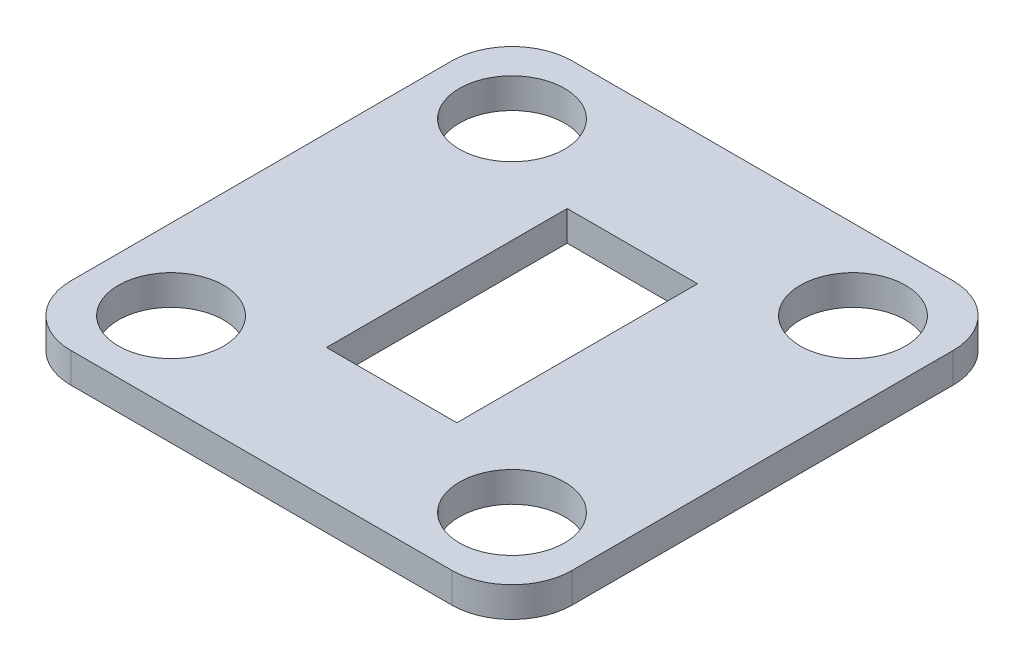
SolidWorks part; units mm, degrees
ref_plane "Front Plane" through (0, 0, 0) normal (0, 0, 1) x (1, 0, 0)
ref_plane "Top Plane" through (0, 0, 0) normal (0, 1, 0) x (1, 0, 0)
ref_plane "Right Plane" through (0, 0, 0) normal (1, 0, 0) x (0, 0, -1)
sketch "Sketch1" plane through (0, 0, 0) normal (0, 1, 0) x (1, 0, 0)
  line L1 (-25, 25) -> (25, 25)
  line L2 (-25, 25) -> (-25, -25)
  line L3 (-25, -25) -> (25, -25)
  line L4 (25, 25) -> (25, -25)
  line L5 (-25, 25) -> (25, -25) construction
  line L6 (-25, -25) -> (25, 25) construction
  point P0 (0, 0)
  dimension "D1" = 50
extrude "Boss-Extrude1" add sketch "Sketch1" along normal mid plane 3
sketch "Sketch2" plane through (0, 1.5, 0) normal (0, 1, 0) x (1, 0, 0)
  line L0 (0, 0) -> (0, -10.2619) construction
  line L1 (0, 0) -> (-11.9708, 0) construction
  circle A0 centre (17, -17) radius 5.25
  circle A1 centre (-17, -17) radius 5.25
  circle A2 centre (-17, 17) radius 5.25
  circle A3 centre (17, 17) radius 5.25
  dimension "D1" = 10.5
  dimension "D2" = 17
  dimension "D3" = 17
extrude "Cut-Extrude1" cut sketch "Sketch2" against normal up to surface (3 mm away) up to face at (0, -1.5, 0)
fillet "Fillet1" radius 6 4 edges at (25, 0, -25) (-25, 0, -25) (-25, 0, 25) (25, 0, 25)
sketch "Sketch3" plane through (0, -1.5, 0) normal (0, -1, 0) x (1, 0, 0)
  line L1 (-6.5, -12) -> (6.5, -12)
  line L2 (-6.5, -12) -> (-6.5, 12)
  line L3 (-6.5, 12) -> (6.5, 12)
  line L4 (6.5, -12) -> (6.5, 12)
  line L5 (-6.5, -12) -> (6.5, 12) construction
  line L6 (-6.5, 12) -> (6.5, -12) construction
  point P0 (0, 0)
  dimension "D1" = 24
  dimension "D2" = 13
extrude "Cut-Extrude2" cut sketch "Sketch3" against normal up to surface (3 mm away) up to face at (17, 1.5, -22.25)
